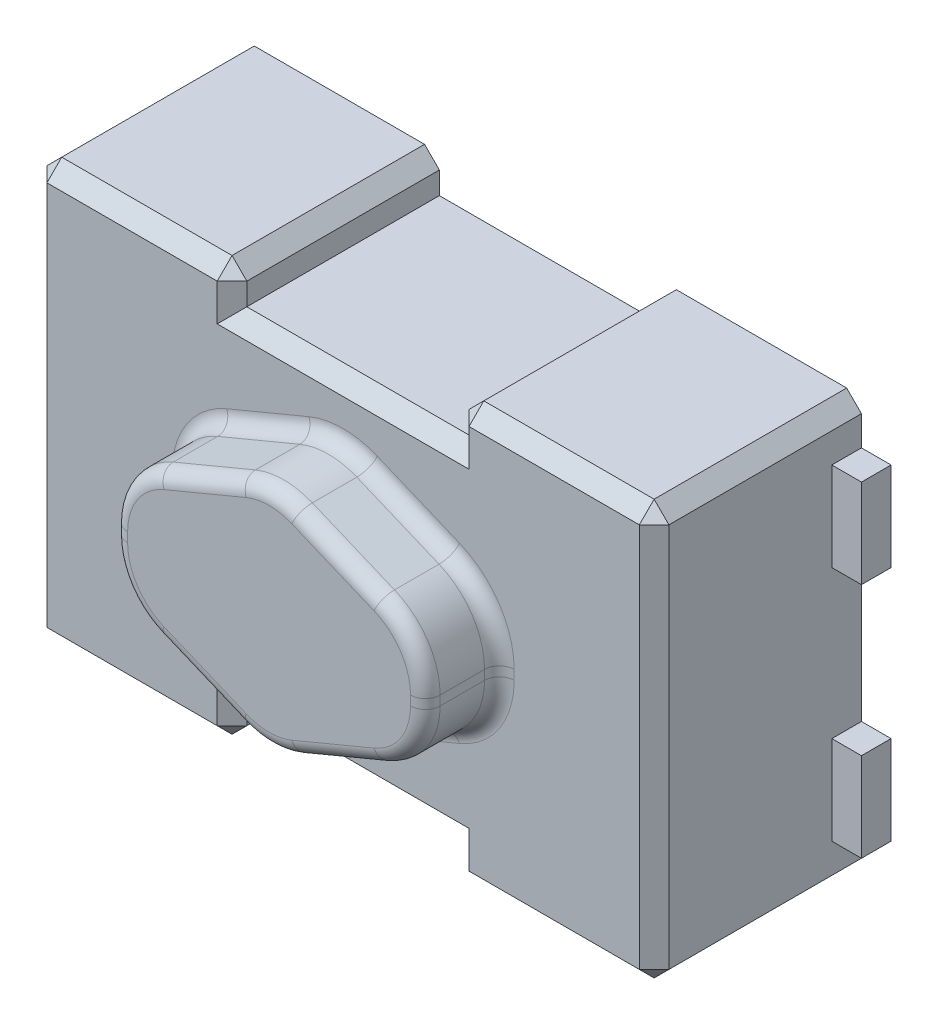
SolidWorks part; units mm, degrees
ref_plane "Front Plane" through (0, 0, 0) normal (0, 0, 1) x (1, 0, 0)
ref_plane "Top Plane" through (0, 0, 0) normal (0, 1, 0) x (1, 0, 0)
ref_plane "Right Plane" through (0, 0, 0) normal (1, 0, 0) x (0, 0, -1)
sketch "Sketch1" plane through (0, 0, 0) normal (0, 0, 1) x (1, 0, 0)
  line L1 (0, 0) -> (4.2, 0)
  line L2 (0, 0) -> (0, 2.8)
  line L3 (0, 2.8) -> (4.2, 2.8)
  line L4 (4.2, 0) -> (4.2, 2.8)
  dimension "D1" = 2.8
  dimension "D2" = 4.2
extrude "Boss-Extrude1" add sketch "Sketch1" along normal blind 1.4
sketch "Sketch2" plane through (0, 0, 0) normal (0, 0, 1) x (1, 0, 0)
  line L0 (0, 1.4) -> (4.2, 1.4) construction
  line L1 (0, 2.8) -> (0, 0) construction
  line L2 (4.2, 0) -> (4.2, 2.8) construction
  line L4 (4.2, 2.5) -> (4.4, 2.5)
  line L5 (4.2, 2.5) -> (4.2, 1.9)
  line L6 (4.2, 1.9) -> (4.4, 1.9)
  line L7 (4.4, 2.5) -> (4.4, 1.9)
  line L8 (4.2, 0.9) -> (4.4, 0.9)
  line L9 (4.2, 0.9) -> (4.2, 0.3)
  line L10 (4.2, 0.3) -> (4.4, 0.3)
  line L11 (4.4, 0.9) -> (4.4, 0.3)
  line L12 (0, 2.5) -> (-0.2, 2.5)
  line L13 (0, 2.5) -> (0, 1.9)
  line L14 (0, 1.9) -> (-0.2, 1.9)
  line L15 (-0.2, 2.5) -> (-0.2, 1.9)
  line L16 (0, 0.9) -> (-0.2, 0.9)
  line L17 (0, 0.9) -> (0, 0.3)
  line L18 (0, 0.3) -> (-0.2, 0.3)
  line L19 (-0.2, 0.9) -> (-0.2, 0.3)
  dimension "D1" = 4.6
  dimension "D2" = 0.6
  dimension "D3" = 1
extrude "Boss-Extrude2" add sketch "Sketch2" along normal blind 0.2
sketch "Sketch3" plane through (0, 0, 1.4) normal (0, 0, 1) x (1, 0, 0)
  line L0 (4.2, 2.8) -> (0, 2.8) construction
  line L1 (1.35, 2.8) -> (2.85, 2.8)
  line L2 (1.35, 2.8) -> (1.35, 2.55)
  line L3 (1.35, 2.55) -> (2.85, 2.55)
  line L4 (2.85, 2.8) -> (2.85, 2.55)
  line L5 (0, 0) -> (4.2, 0) construction
  line L6 (1.35, 0) -> (2.85, 0)
  line L7 (1.35, 0) -> (1.35, 0.25)
  line L8 (1.35, 0.25) -> (2.85, 0.25)
  line L9 (2.85, 0) -> (2.85, 0.25)
  line L10 (2.1, 2.8) -> (2.1, 0) construction
  point P14 (2.1, 2.8)
  point P15 (2.1, 2.55)
  point P16 (2.1, 0.25)
  dimension "D1" = 1.5
  dimension "D2" = 0.25
extrude "Cut-Extrude1" cut sketch "Sketch3" against normal through all
sketch "Sketch4" plane through (0, 0, 1.4) normal (0, 0, 1) x (1, 0, 0)
  line L0 (0, 1.4) -> (4.2, 1.4) construction
  line L1 (0, 2.8) -> (0, 0) construction
  line L2 (4.2, 0) -> (4.2, 2.8) construction
  line L4 (1.35, 2.55) -> (2.85, 2.55) construction
  line L5 (2.1, 2.55) -> (2.1, 0.25) construction
  line L6 (2.85, 0.25) -> (1.35, 0.25) construction
  line L7 (2.1, 2.205) -> (1.045, 1.7653)
  line L8 (1.045, 1.7653) -> (1.045, 1.0347)
  line L9 (1.045, 1.0347) -> (2.1, 0.595)
  line L10 (2.1, 0.595) -> (3.155, 1.0347)
  line L11 (3.155, 1.0347) -> (3.155, 1.7653)
  line L12 (3.155, 1.7653) -> (2.1, 2.205)
  point P6 (3.155, 1.4)
  point P13 (1.045, 1.4)
  dimension "D1" = 1.61
  dimension "D2" = 2.11
  dimension "D3" = 0.7305
extrude "Boss-Extrude3" add sketch "Sketch4" along normal blind 0.5
fillet "Fillet1" radius 0.5 6 edges at (2.1, 2.205, 1.65) (1.045, 1.7653, 1.65) (3.155, 1.7653, 1.65) (3.155, 1.0347, 1.65) (1.045, 1.0347, 1.65) (2.1, 0.595, 1.65)
fillet "Fillet2" radius 0.1 24 edges at (1.129, 1.0907, 1.4) (1.045, 1.4, 1.4) (1.129, 1.7093, 1.4) (1.6301, 2.0092, 1.4) (2.1, 2.1633, 1.4) (2.5699, 2.0092, 1.4) (3.071, 1.7093, 1.4) (3.155, 1.4, 1.4) (3.071, 1.0907, 1.4) (2.5699, 0.7908, 1.4) (2.1, 0.6367, 1.4) (1.129, 1.0907, 1.9) (1.045, 1.4, 1.9) (1.129, 1.7093, 1.9) (1.6301, 2.0092, 1.9) (2.1, 2.1633, 1.9) (2.5699, 2.0092, 1.9) (3.071, 1.7093, 1.9) (3.155, 1.4, 1.9) (3.071, 1.0907, 1.9) (2.5699, 0.7908, 1.9) (2.1, 0.6367, 1.9) (1.6301, 0.7908, 1.4) (1.6301, 0.7908, 1.9)
chamfer "Chamfer1" distance 0.1 angle 45 20 edges at (4.2, 2.8, 0.7) (2.85, 2.8, 0.7) (1.35, 2.8, 0.7) (0, 2.8, 0.7) (0, 0, 0.7) (1.35, 0, 0.7) (2.85, 0, 0.7) (4.2, 0, 0.7) (4.2, 1.4, 1.4) (3.525, 2.8, 1.4) (2.85, 2.675, 1.4) (2.1, 2.55, 1.4) (1.35, 2.675, 1.4) (0.675, 2.8, 1.4) (0, 1.4, 1.4) (3.525, 0, 1.4) (2.85, 0.125, 1.4) (2.1, 0.25, 1.4) (1.35, 0.125, 1.4) (0.675, 0, 1.4)
